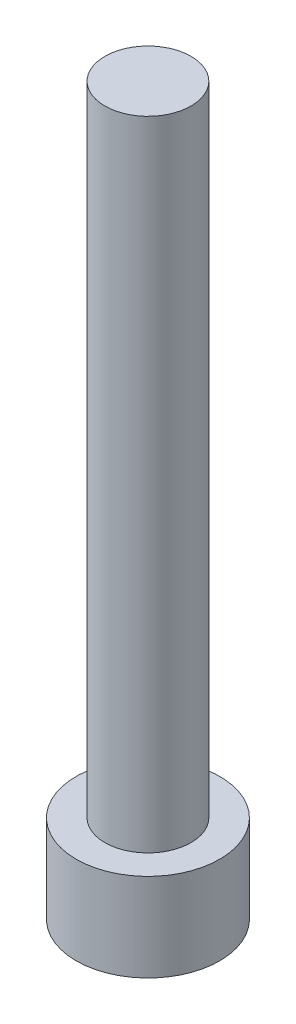
SolidWorks part; units mm, degrees
ref_plane "Front Plane" through (0, 0, 0) normal (0, 0, 1) x (1, 0, 0)
ref_plane "Top Plane" through (0, 0, 0) normal (0, 1, 0) x (1, 0, 0)
ref_plane "Right Plane" through (0, 0, 0) normal (1, 0, 0) x (0, 0, -1)
sketch "Sketch1" plane through (0, 0, 0) normal (0, 1, 0) x (1, 0, 0)
  circle A0 centre (0, 0) radius 2.8575
  dimension "D1" = 5.715
extrude "Boss-Extrude1" add sketch "Sketch1" along normal blind 3.5052
sketch "Sketch2" plane through (0, 0, 0) normal (0, -1, 0) x (1, 0, 0)
  line L1 (1.604, 0) -> (0.802, 1.3891)
  line L2 (0.802, 1.3891) -> (-0.802, 1.3891)
  line L3 (-0.802, 1.3891) -> (-1.604, 0)
  line L4 (-1.604, 0) -> (-0.802, -1.3891)
  line L5 (-0.802, -1.3891) -> (0.802, -1.3891)
  line L6 (0.802, -1.3891) -> (1.604, 0)
  circle A0 centre (0, 0) radius 1.3891 construction
  dimension "D1" = 2.7781
extrude "Cut-Extrude1" cut sketch "Sketch2" against normal blind 1.9558
sketch "Sketch3" plane through (0, 3.5052, 0) normal (0, 1, 0) x (1, 0, 0)
  circle A0 centre (0, 0) radius 1.7145
  dimension "D1" = 3.429
extrude "Boss-Extrude2" add sketch "Sketch3" along normal blind 25.4
